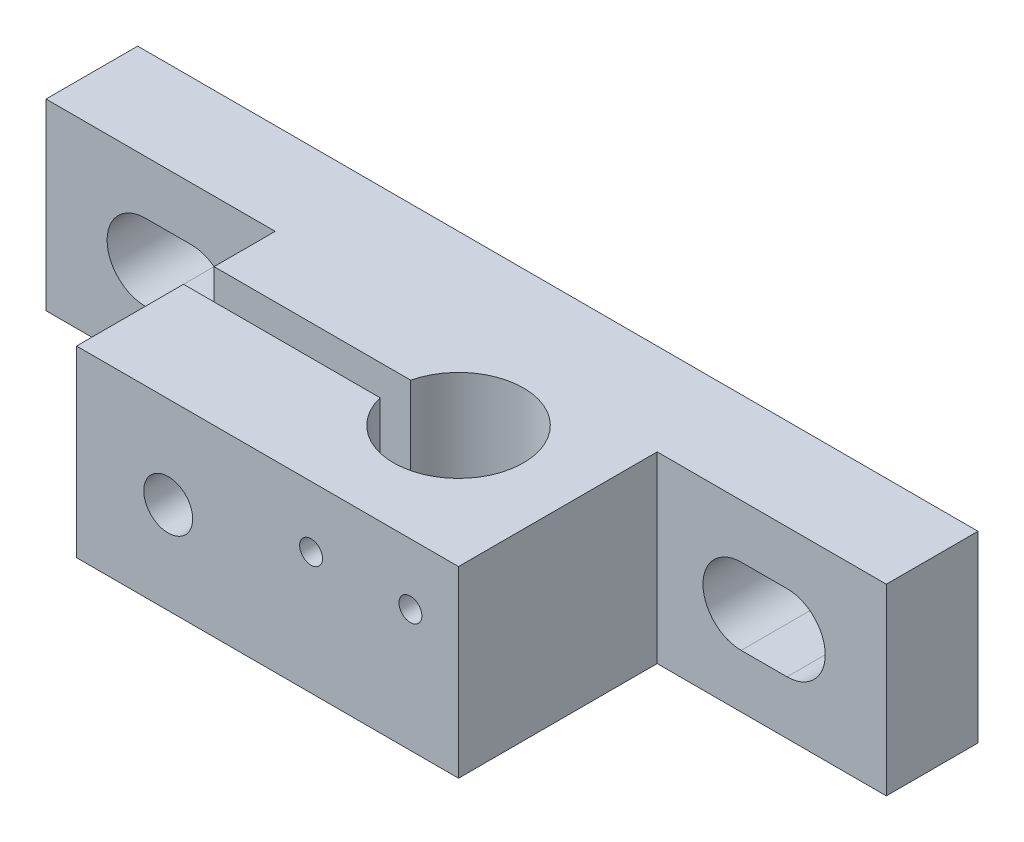
SolidWorks part; units mm, degrees
material "Copper"
ref_plane "Front Plane" through (0, 0, 0) normal (0, 0, 1) x (1, 0, 0)
ref_plane "Top Plane" through (0, 0, 0) normal (0, 1, 0) x (1, 0, 0)
ref_plane "Right Plane" through (0, 0, 0) normal (1, 0, 0) x (0, 0, -1)
sketch "Sketch2" plane through (0, 0, 0) normal (0, 0, 1) x (1, 0, 0)
  line L0 (6.5, 6) -> (9.5, 6) construction
  line L1 (0, 0) -> (55, 0)
  line L2 (0, 0) -> (0, 12)
  line L3 (0, 12) -> (55, 12)
  line L4 (55, 0) -> (55, 12)
  line L5 (27.5, 12) -> (27.5, -3.75) construction
  line L6 (6.5, 8.5) -> (9.5, 8.5)
  line L7 (6.5, 3.5) -> (9.5, 3.5)
  line L8 (48.5, 6) -> (45.5, 6) construction
  line L9 (48.5, 8.5) -> (45.5, 8.5)
  line L10 (48.5, 3.5) -> (45.5, 3.5)
  arc A0 (6.5, 8.5) -> (6.5, 3.5) centre (6.5, 6) ccw
  arc A1 (48.5, 8.5) -> (48.5, 3.5) centre (48.5, 6) cw
  arc A2 (9.5, 3.5) -> (9.5, 8.5) centre (9.5, 6) ccw
  arc A3 (45.5, 3.5) -> (45.5, 8.5) centre (45.5, 6) cw
  point P11 (8, 6)
  point P16 (47, 6)
  dimension "D1" = 6.5
  dimension "D2" = 3
  dimension "D5" = 55
extrude "Boss-Extrude1" add sketch "Sketch2" along normal blind 6
sketch "Sketch3" plane through (0, 0, 6) normal (0, 0, 1) x (1, 0, 0)
  line L0 (0, 0) -> (55, 0) construction
  line L1 (15, 0) -> (40, 0)
  line L2 (15, 0) -> (15, 12)
  line L3 (15, 12) -> (40, 12)
  line L4 (40, 0) -> (40, 12)
  line L5 (55, 12) -> (0, 12) construction
  line L6 (0, 12) -> (0, 0) construction
  line L7 (55, 0) -> (55, 12) construction
  dimension "D1" = 25
  dimension "D2" = 15
  dimension "D3" = 15
extrude "Boss-Extrude2" add sketch "Sketch3" along normal blind 13
sketch "Sketch4" plane through (0, 0, 0) normal (0, -1, 0) x (1, 0, 0)
  line L0 (15, 19) -> (40, 19) construction
  line L1 (40, 19) -> (40, 6) construction
  line L2 (0, 0) -> (55, 0) construction
  line L3 (27.8693, 12) -> (15, 12)
  line L4 (15, 19) -> (15, 6) construction
  line L5 (15, 12) -> (15, 10)
  line L6 (15, 10) -> (27.8693, 10)
  circle A0 centre (32, 11) radius 4.25
  line M4 (15, 19) -> (15, 6)
  dimension "D1" = 8
  dimension "D5" = 8.5
  dimension "D7" = 11
  dimension "D2" = 8
  dimension "D3" = 11
  dimension "D4" = 1
  dimension "D6" = 1
extrude "Cut-Extrude2" cut sketch "Sketch4" against normal blind 30 contours A0 L3 L6 M4 | A0
sketch "Sketch5" plane through (0, 0, 0) normal (0, 0, -1) x (-1, 0, 0)
  line L0 (-55, 12) -> (0, 12) construction
  line L1 (-37.6724, 9.5) -> (-17.1585, 9.5)
  line L2 (-37.6724, 9.5) -> (-37.6724, 2.5)
  line L3 (-37.6724, 2.5) -> (-17.1585, 2.5)
  line L4 (-17.1585, 9.5) -> (-17.1585, 2.5)
  line L5 (0, 0) -> (-55, 0) construction
  line L6 (0, 12) -> (0, 0) construction
  dimension "D1" = 20.5139
  dimension "D2" = 2.5
  dimension "D3" = 2.5
  dimension "D4" = 17.1585
extrude "Cut-Extrude3" cut sketch "Sketch5" against normal blind 5
sketch "Sketch6" plane through (0, 0, 19) normal (0, 0, 1) x (1, 0, 0)
  line L0 (15, 12) -> (15, 0) construction
  line L1 (40, 12) -> (15, 12) construction
  line L2 (15, 0) -> (40, 0) construction
  circle A0 centre (21, 6) radius 1.6
  dimension "D1" = 6
  dimension "D2" = 6
  dimension "D3" = 6
extrude "Cut-Extrude4" cut sketch "Sketch6" against normal blind 11
sketch "Sketch7" plane through (0, 0, 5) normal (0, 0, -1) x (-1, 0, 0)
  line L1 (-17.5359, 6) -> (-19.2679, 9)
  line L2 (-19.2679, 9) -> (-22.7321, 9)
  line L3 (-22.7321, 9) -> (-24.4641, 6)
  line L4 (-24.4641, 6) -> (-22.7321, 3)
  line L5 (-22.7321, 3) -> (-19.2679, 3)
  line L6 (-19.2679, 3) -> (-17.5359, 6)
  circle A0 centre (-21, 6) radius 3 construction
extrude "Cut-Extrude5" cut sketch "Sketch7" against normal blind 3
sketch "Sketch8" plane through (0, 0, 19) normal (0, 0, 1) x (1, 0, 0)
  line L0 (40, 0) -> (40, 12) construction
  line L1 (40, 12) -> (15, 12) construction
  circle A0 centre (36.85, 8) radius 0.75
  circle A1 centre (30.35, 8) radius 0.75
  dimension "D1" = 1.5
  dimension "D2" = 3.15
  dimension "D3" = 4
  dimension "D4" = 2
extrude "Cut-Extrude6" cut sketch "Sketch8" against normal blind 3
